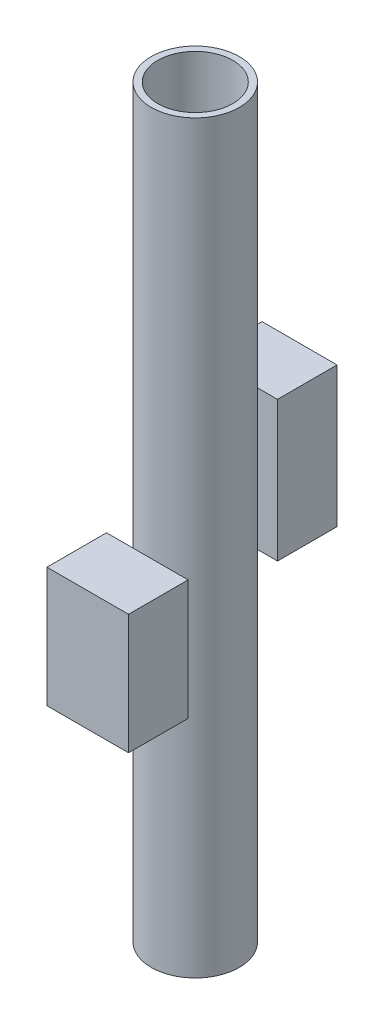
SolidWorks part; units mm, degrees
ref_plane "Front Plane" through (0, 0, 0) normal (0, 0, 1) x (1, 0, 0)
ref_plane "Top Plane" through (0, 0, 0) normal (0, 1, 0) x (1, 0, 0)
ref_plane "Right Plane" through (0, 0, 0) normal (1, 0, 0) x (0, 0, -1)
sketch "Sketch1" plane through (0, 0, 0) normal (0, 1, 0) x (1, 0, 0)
  circle A0 centre (0, 0) radius 14.7873
extrude "Boss-Extrude1" add sketch "Sketch1" along normal blind 250
sketch "Sketch2" plane through (0, 250, 0) normal (0, 1, 0) x (1, 0, 0)
  circle A0 centre (0, 0) radius 12.5941
extrude "Cut-Extrude1" cut sketch "Sketch2" against normal blind 250
ref_plane "Plane2" through (0, 125, 0) normal (0, 1, 0) x (1, 0, 0)
ref_plane "Plane3" through (0, 100, 0) normal (0, 1, 0) x (1, 0, 0)
sketch "Sketch4" plane through (0, 125, 0) normal (0, 1, 0) x (1, 0, 0)
  circle A0 centre (0, 0) radius 12.5941
extrude "Boss-Extrude2" add sketch "Sketch4" along normal mid plane 3
sketch "Sketch5" plane through (0, 100, 0) normal (0, 1, 0) x (1, 0, 0)
  circle A0 centre (0, 0) radius 12.5941
extrude "Boss-Extrude3" add sketch "Sketch5" along normal mid plane 3
ref_plane "Plane4" through (0, 0, 15) normal (0, 0, 1) x (1, 0, 0)
sketch "Sketch7" plane through (0, 0, 15) normal (0, 0, 1) x (1, 0, 0)
  line L0 (-14.7873, 119.0725) -> (12.5941, 119.0725)
  line L1 (-14.7873, 250) -> (-14.7873, 0) construction
  line L2 (12.5941, 0) -> (12.5941, 98.5) construction
  line L3 (12.5941, 119.0725) -> (12.5941, 78.8043)
  line L5 (-14.7873, 78.8043) -> (-14.7873, 119.0725)
  line L6 (-14.7873, 78.8043) -> (12.5941, 78.8043)
extrude "Boss-Extrude4" add sketch "Sketch7" along normal blind 20 separate body
ref_plane "Plane5" through (0, 0, -15) normal (0, 0, 1) x (1, 0, 0)
sketch "Sketch8" plane through (0, 0, -15) normal (0, 0, 1) x (1, 0, 0)
  line L0 (12.5941, 156.5481) -> (-12.5941, 156.5481)
  line L2 (-12.5941, 250) -> (-12.5941, 126.5) construction
  line L3 (-12.5941, 156.5481) -> (-12.5941, 109.5304)
  line L4 (-12.5941, 123.5) -> (-12.5941, 101.5) construction
  line L5 (-12.5941, 109.5304) -> (12.5941, 109.5304)
  line L6 (12.5941, 101.5) -> (12.5941, 123.5) construction
  line L7 (12.5941, 109.5304) -> (12.5941, 156.5481)
  line L8 (12.5941, 126.5) -> (12.5941, 250) construction
extrude "Boss-Extrude5" add sketch "Sketch8" against normal blind 20 separate body
